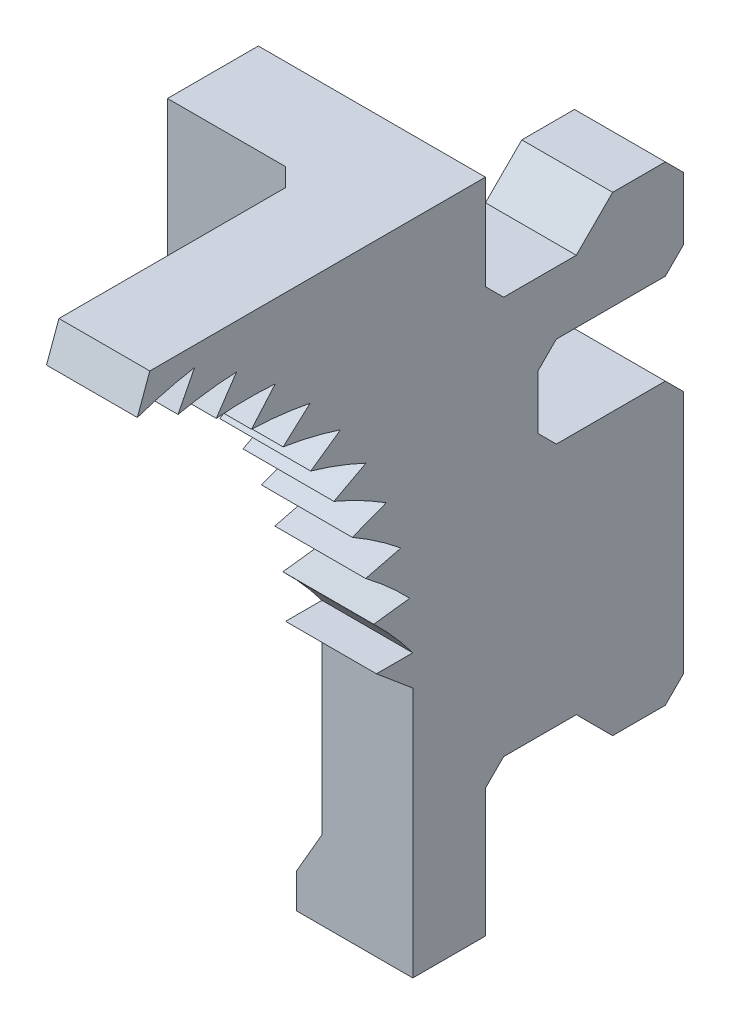
SolidWorks part; units mm, degrees
ref_plane "前视基准面" through (0, 0, 0) normal (0, 0, 1) x (1, 0, 0)
ref_plane "上视基准面" through (0, 0, 0) normal (0, 1, 0) x (1, 0, 0)
ref_plane "右视基准面" through (0, 0, 0) normal (1, 0, 0) x (0, 0, -1)
other "Configuration Table"
sketch "草图1" plane through (0, 0, 0) normal (1, 0, 0) x (0, 0, -1)
  line L0 (0, 0) -> (4, 0)
  line L1 (4, 0) -> (4, 36.1732)
  line L2 (4, 36.1732) -> (0, 36.1732)
  line L3 (0, 36.1732) -> (0, 0) construction
  line L4 (0, 0) -> (-12963.8243, 0) construction
  line L5 (-2, 15.5) -> (0, 15.5)
  line L6 (-2.1491, 17.9374) -> (-22, 15.5) construction
  line L7 (-22, 15.5) -> (-2, 15.5) construction
  line L8 (-2.1491, 17.9374) -> (-0.164, 18.1811)
  line L9 (-2.5941, 20.3384) -> (-0.6535, 20.8223)
  line L10 (-3.3284, 22.6674) -> (-1.4612, 23.3841)
  line L11 (-4.341, 24.8894) -> (-2.5752, 25.8284)
  line L12 (-5.617, 26.9715) -> (-3.9787, 28.1187)
  line L13 (-7.1371, 28.8826) -> (-5.6508, 30.2209)
  line L14 (-8.8788, 30.5942) -> (-7.5667, 32.1036)
  line L15 (-10.8161, 32.0808) -> (-9.6978, 33.7388)
  line L16 (-12.9202, 33.3201) -> (-12.0122, 35.1021)
  line L17 (-22, 15.5) -> (-2.5941, 20.3384) construction
  line L18 (-14.4756, 36.1732) -> (-15.1596, 34.2939)
  line L19 (-14.4756, 36.1732) -> (0, 36.1732)
  line L20 (0, 0) -> (0, 13.8218)
  line L21 (0, 13.8218) -> (-2, 15.5)
  circle A0 centre (-22, 15.5) radius 20 construction
  arc A1 (0, 15.5) -> (-2.1491, 17.9374) centre (-16.0265, 3.5354) ccw
  arc A2 (-0.164, 18.1811) -> (-2.5941, 20.3384) centre (-14.6129, 4.3525) ccw
  arc A3 (-0.6535, 20.8223) -> (-3.3284, 22.6674) centre (-13.3094, 5.3359) ccw
  arc A4 (-1.4612, 23.3841) -> (-4.341, 24.8894) centre (-12.1355, 6.4708) ccw
  arc A5 (-2.5752, 25.8284) -> (-5.617, 26.9715) centre (-11.1086, 7.7403) ccw
  arc A6 (-3.9787, 28.1187) -> (-7.1371, 28.8826) centre (-10.2441, 9.1254) ccw
  arc A7 (-5.6508, 30.2209) -> (-8.8788, 30.5942) centre (-9.5549, 10.6056) ccw
  arc A8 (-7.5667, 32.1036) -> (-10.8161, 32.0808) centre (-9.0512, 12.1588) ccw
  arc A9 (-9.6978, 33.7388) -> (-12.9202, 33.3201) centre (-8.7405, 13.7617) ccw
  arc A10 (-12.0122, 35.1021) -> (-15.1596, 34.2939) centre (-8.6275, 15.3906) ccw
  point P52 (-22, 15.5)
  dimension "D2" = 40
  dimension "D5" = 20
  dimension "D1" = 15.5
  dimension "D3" = 22
  dimension "D4" = 4
  dimension "D6" = 7
  dimension "D8" = 7
  dimension "D10" = 50
  dimension "D7" = 10
extrude "凸台-拉伸1" add sketch "草图1" along normal mid plane 5 contours A10 L16 A9 L15 A8 L14 A7 L13 A6 L12 A5 L11 A4 L10 A3 L9 A2 L8 A1 L5 L21 L20 L0 L1 L2 L19 L18
sketch "草图5" plane through (0, 0, -4) normal (0, 0, -1) x (-1, 0, 0)
  circle A0 centre (0, 20) radius 2.1
  dimension "D1" = 4.2
  dimension "D2" = 20
extrude "切除-拉伸2" [suppressed] cut sketch "草图5" against normal blind 1
sketch "草图6" plane through (0, 0, 0) normal (1, 0, 0) x (0, 0, -1)
  line L0 (4, 0) -> (14.9, 0) construction
  line L1 (14.9, 0) -> (14.9, 31.95) construction
  line L2 (14.9, 31.95) -> (11, 31.95)
  line L3 (11, 31.95) -> (9, 29.95)
  line L4 (9, 29.95) -> (5, 29.95)
  line L5 (4, 30.95) -> (4, 7.05)
  line L6 (5, 29.95) -> (4, 30.95)
  line L7 (4, 0) -> (4, 36.1732) construction
  line L8 (4, 30.95) -> (4, 0) construction
  line L9 (4, 7.05) -> (5, 8.05)
  line L10 (5, 8.05) -> (9, 8.05)
  line L11 (9, 8.05) -> (11, 6.05)
  line L12 (11, 6.05) -> (14.9, 6.05)
  line L13 (14.9, 6.05) -> (14.9, 31.95)
  line L14 (14.9, 19) -> (50014.9, 19) construction
  point P5 (14.9, 19)
  dimension "D1" = 1
  dimension "D2" = 31.95
  dimension "D3" = 2
  dimension "D4" = 45
  dimension "D5" = 3.9
  dimension "D6" = 4
  dimension "D7" = 6.05
extrude "凸台-拉伸2" add sketch "草图6" along normal up to surface and the other way up to surface
sketch "草图8" plane through (0, 0, 0) normal (0, 0, 1) x (1, 0, 0)
  line L0 (-2.5, 0) -> (-3.9, 0)
  line L1 (-3.9, 0) -> (-3.9, 1.9)
  line L2 (-3.9, 1.9) -> (-2.5, 4.3249)
  line L3 (-2.5, 0) -> (-2.5, 13.8218) construction
  line L4 (-2.5, 4.3249) -> (-2.5, 0)
  dimension "D1" = 30
  dimension "D2" = 1.4
  dimension "D3" = 1.9
extrude "凸台-拉伸4" add sketch "草图8" against normal up to surface (4 mm away) up to face at (0, 3.525, -4)
sketch "草图9" plane through (0, 0, -14.9) normal (0, 0, -1) x (-1, 0, 0)
  line L1 (2.5, 31.95) -> (2.5, 6.05) construction
  line L2 (-2.5, 26.5) -> (2.5, 26.5)
  line L3 (-2.5, 26.5) -> (-2.5, 21.5)
  line L4 (-2.5, 21.5) -> (2.5, 21.5)
  line L5 (2.5, 26.5) -> (2.5, 21.5)
  line L6 (-2.5, 26.5) -> (2.5, 21.5) construction
  line L7 (-2.5, 21.5) -> (2.5, 26.5) construction
  line L8 (-2.5, 6.05) -> (-2.5, 31.95) construction
  circle A0 centre (0, 24) radius 1.65
  dimension "D1" = 3.3
  dimension "D2" = 5
  dimension "D3" = 24
extrude "切除-拉伸4" cut sketch "草图9" against normal blind 8 contours L4 L5 L2 L3
sketch "草图10" plane through (0, 0, 0) normal (1, 0, 0) x (0, 0, -1)
  line L0 (4, 30.95) -> (4, 36.1732) construction
  line L1 (4, 24) -> (-1, 24)
  line L2 (4, 24) -> (4, 36.1732)
  line L3 (4, 36.1732) -> (-1, 36.1732)
  line L4 (-1, 24) -> (-1, 36.1732)
  line L5 (4, 36.1732) -> (-14.4756, 36.1732) construction
  dimension "D1" = 5
  dimension "D2" = 24
extrude "凸台-拉伸5" add sketch "草图10" against normal blind 10
chamfer "倒角2" distance 1 angle 45 6 edges at (0, 21.5, -6.9) (0, 26.5, -6.9) (0, 21.5, -14.9) (0, 26.5, -14.9) (0, 6.05, -14.9) (0, 31.95, -14.9)
chamfer "倒角3" distance 1 angle 45 2 edges at (-2.5, 30.0866, 1) (-2.5, 27.475, -4)
equation "\"D8@草图1\"=\"D6@草图1\""
